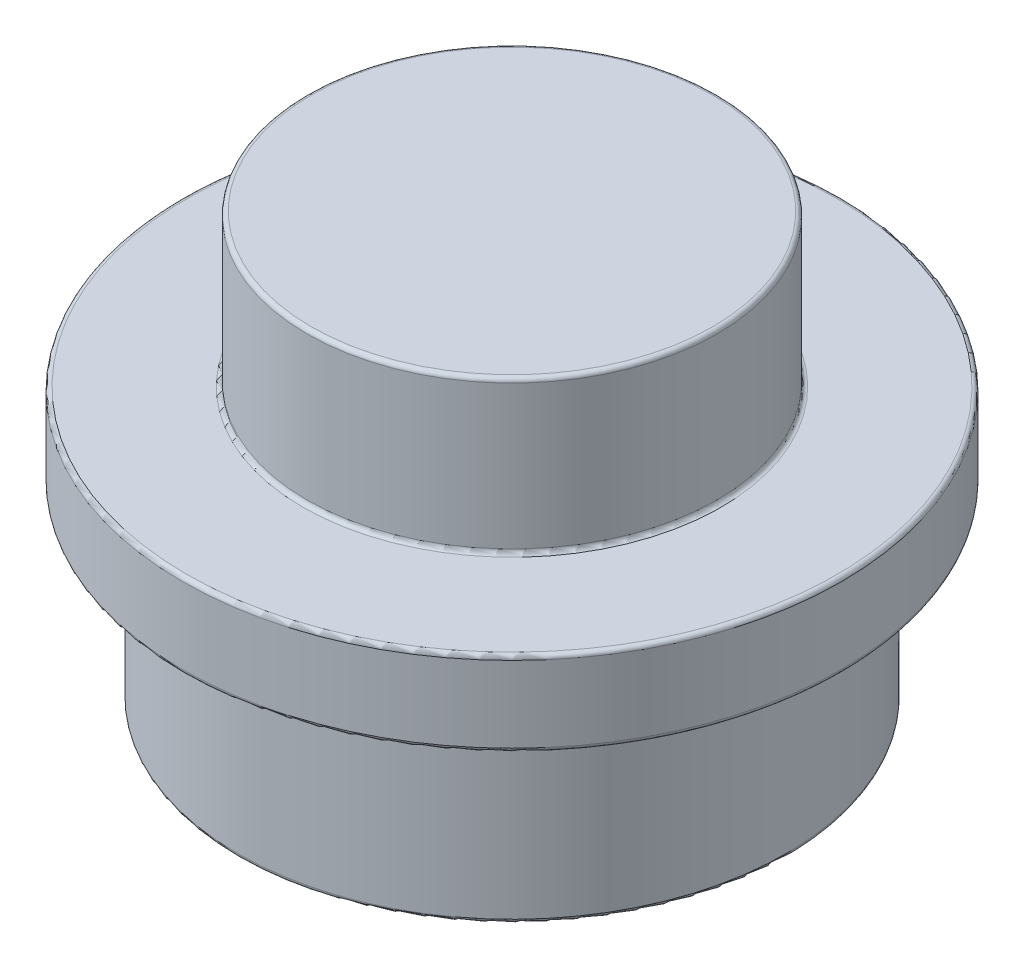
SolidWorks part; units mm, degrees
ref_plane "Front Plane" through (0, 0, 0) normal (0, 0, 1) x (1, 0, 0)
ref_plane "Top Plane" through (0, 0, 0) normal (0, 1, 0) x (1, 0, 0)
ref_plane "Right Plane" through (0, 0, 0) normal (1, 0, 0) x (0, 0, -1)
sketch "Sketch1" plane through (0, 0, 0) normal (0, 1, 0) x (1, 0, 0)
  circle A0 centre (0, 0) radius 3.9
  dimension "D1" = 7.8
extrude "Extrude1" add sketch "Sketch1" along normal blind 3.22
sketch "Sketch2" plane through (0, 3.22, 0) normal (0, 1, 0) x (1, 0, 0)
  circle A0 centre (0, 0) radius 2.425
  dimension "D1" = 4.85
extrude "Extrude2" add sketch "Sketch2" along normal blind 1.8
sketch "Sketch3" plane through (0, 0, 0) normal (0, -1, 0) x (1, 0, 0)
  circle A0 centre (0, 0) radius 3.24
  circle A1 centre (0, 0) radius 3.9 construction
  circle A2 centre (0, 0) radius 3.9
  dimension "D1" = 6.48
extrude "Extrude3" cut sketch "Sketch3" against normal offset from surface (2.22 mm away) 1 up to face at (0, 3.22, 3.9)
shell "Shell1" thickness 1.55
fillet "Fillet1" radius 0.05 10 edges at (0, 0, 1.69) (0, 1.67, 0.875) (0, 3.47, 0.875) (0, 1.67, 1.69) (0, 2.22, 3.9) (0, 0, -3.24) (0, 2.22, 3.24) (0, 3.22, 2.425) (0, 5.02, 2.425) (0, 3.22, 3.9)
